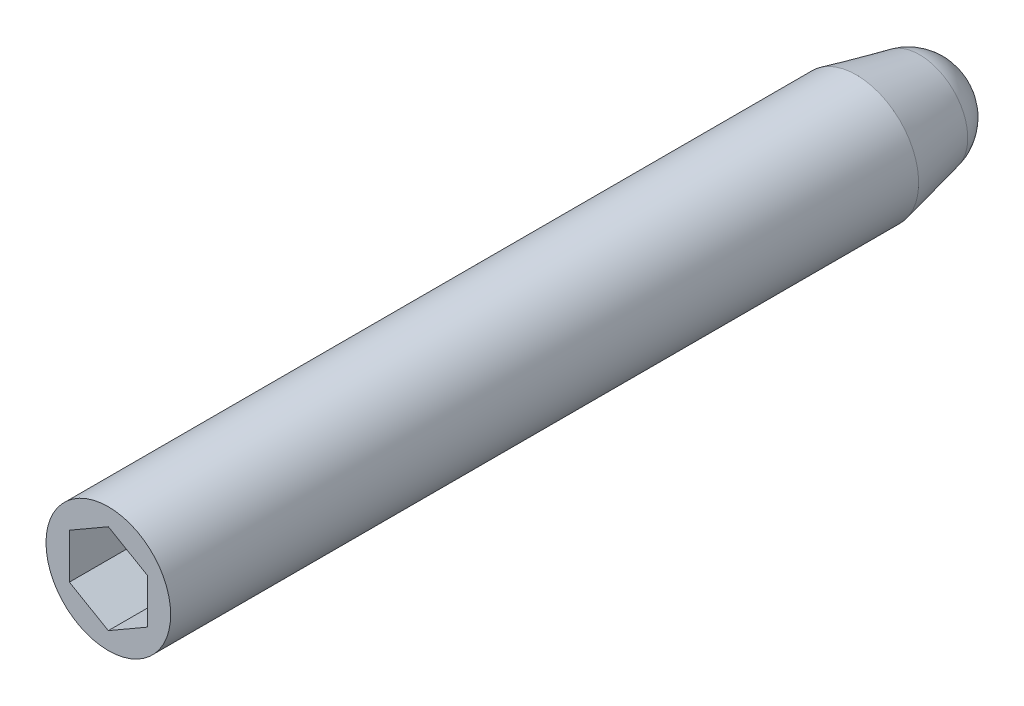
SolidWorks part; units mm, degrees
ref_plane "Front Plane" through (0, 0, 0) normal (0, 0, 1) x (1, 0, 0)
ref_plane "Top Plane" through (0, 0, 0) normal (0, 1, 0) x (1, 0, 0)
ref_plane "Right Plane" through (0, 0, 0) normal (1, 0, 0) x (0, 0, -1)
sketch "Sketch1" plane through (0, 0, 0) normal (0, 0, 1) x (1, 0, 0)
  circle A0 centre (0, 0) radius 3.175
  dimension "D1" = 6.35
extrude "Boss-Extrude1" add sketch "Sketch1" along normal blind 38.1
sketch "Sketch2" plane through (0, 0, 38.1) normal (0, 0, 1) x (1, 0, 0)
  line L1 (0, 2.2914) -> (-1.9844, 1.1457)
  line L2 (-1.9844, 1.1457) -> (-1.9844, -1.1457)
  line L3 (-1.9844, -1.1457) -> (0, -2.2914)
  line L4 (0, -2.2914) -> (1.9844, -1.1457)
  line L5 (1.9844, -1.1457) -> (1.9844, 1.1457)
  line L6 (1.9844, 1.1457) -> (0, 2.2914)
  circle A0 centre (0, 0) radius 1.9844 construction
  dimension "D1" = 3.9688
extrude "Cut-Extrude1" cut sketch "Sketch2" against normal blind 3.175
sketch "Sketch3" plane through (0, 0, 0) normal (0, 1, 0) x (1, 0, 0)
  line L0 (-3.175, 0) -> (-2.4537, 3.2224)
  line L1 (0, 5.08) -> (0, 0)
  line L2 (-3.175, 0) -> (0, 0)
  arc A0 (-2.4537, 3.2224) -> (0, 5.08) centre (-0.13, 2.7023) cw
  dimension "D1" = 2.3813
  dimension "D2" = 5.08
revolve "Revolve1" add sketch "Sketch3" angle 360 about L1
